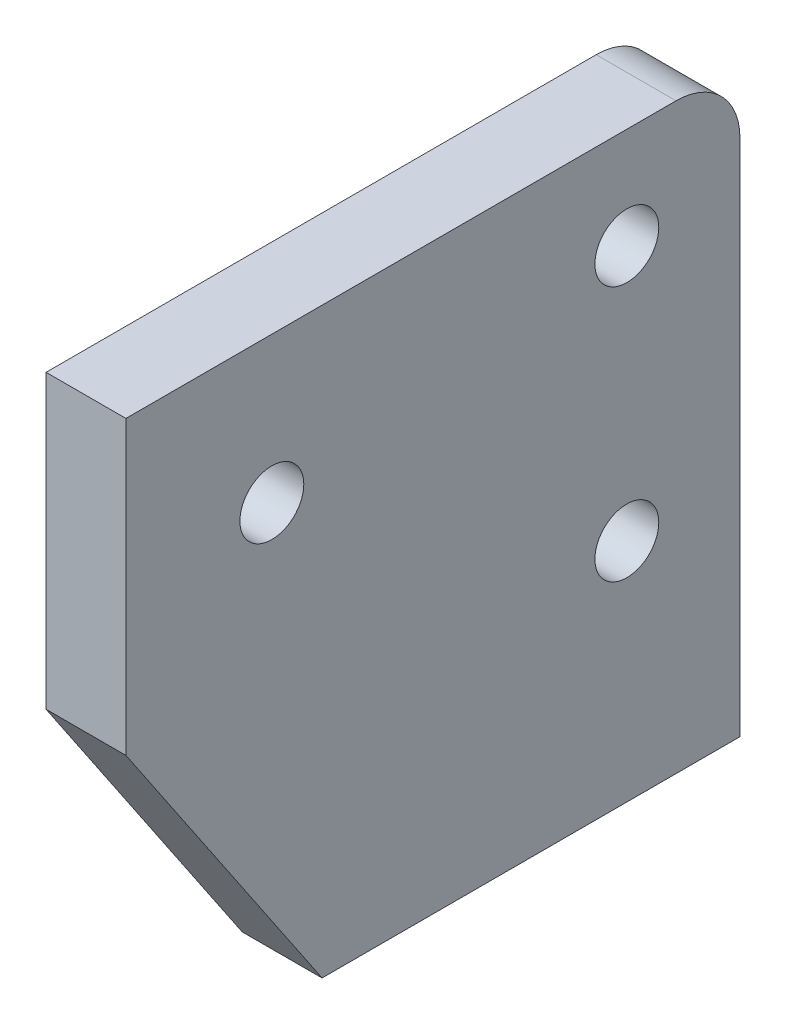
SolidWorks part; units mm, degrees
ref_plane "Front Plane" through (0, 0, 0) normal (0, 0, 1) x (1, 0, 0)
ref_plane "Top Plane" through (0, 0, 0) normal (0, 1, 0) x (1, 0, 0)
ref_plane "Right Plane" through (0, 0, 0) normal (1, 0, 0) x (0, 0, -1)
sketch "Sketch1" plane through (0, 0, 0) normal (1, 0, 0) x (0, 0, -1)
  line L8 (0.8463, 2.6238) -> (9.8401, 2.6238)
  line L9 (9.8401, 2.6238) -> (9.8401, 25.7899)
  line L10 (9.8401, 25.7899) -> (0.8463, 25.7899)
  line L12 (-14.5718, 14.1873) -> (-14.5718, 25.7899)
  line L13 (-14.5718, 25.7899) -> (0.8463, 25.7899)
  line L14 (5.3432, 2.6238) -> (5.3432, 11.6176) construction
  line L15 (5.3432, 11.6176) -> (5.3432, 21.7776) construction
  line L16 (-14.5718, 19.9886) -> (-8.7706, 19.9886) construction
  line L17 (-8.7706, 19.9886) -> (-8.7706, 25.7899) construction
  line L21 (0.8463, 2.6238) -> (-6.7737, 2.6238)
  line L22 (-6.7737, 2.6238) -> (-14.5718, 14.1873)
  circle A0 centre (5.3432, 21.7776) radius 1.27
  circle A1 centre (5.3432, 11.6176) radius 1.27
  circle A2 centre (-8.7706, 19.9886) radius 1.27
  dimension "D3" = 11.6025
  dimension "D1" = 8.9939
  dimension "D2" = 10.16
  dimension "D4" = 5.8013
  dimension "D5" = 23.1661
extrude "Boss-Extrude1" add sketch "Sketch1" along normal blind 3.175
fillet "Fillet3" radius 2.54 1 edges at (1.5875, 25.7899, -9.8401)
